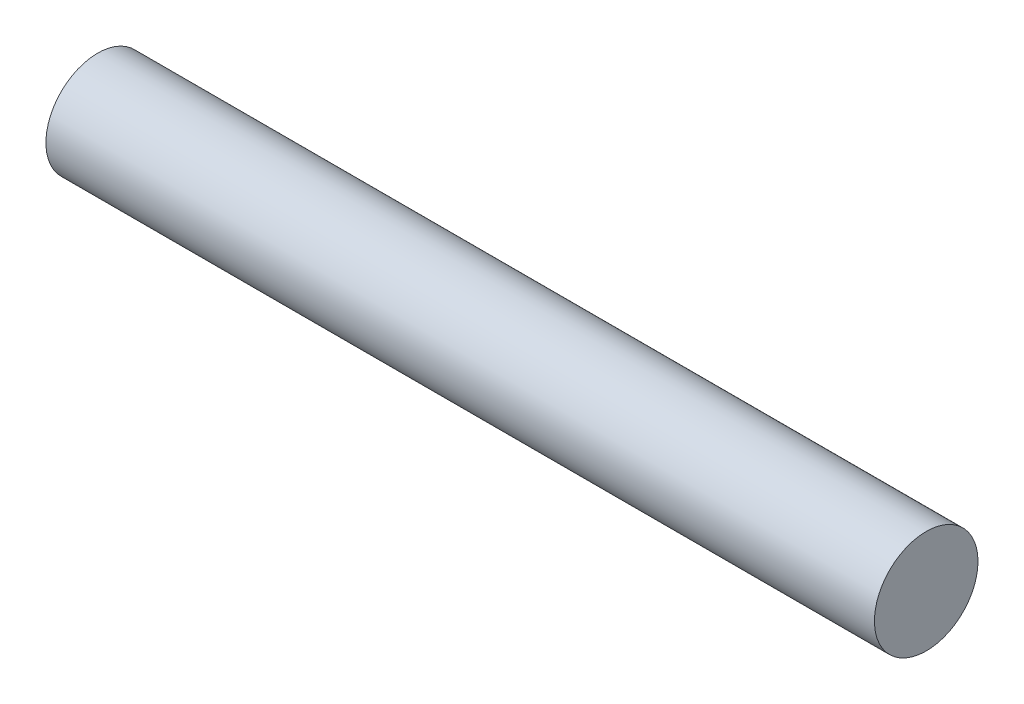
SolidWorks part; units mm, degrees
ref_plane "Plan de face" through (0, 0, 0) normal (0, 0, 1) x (1, 0, 0)
ref_plane "Plan de dessus" through (0, 0, 0) normal (0, 1, 0) x (1, 0, 0)
ref_plane "Plan de droite" through (0, 0, 0) normal (1, 0, 0) x (0, 0, -1)
sketch "Esquisse1" plane through (0, 0, 0) normal (1, 0, 0) x (0, 0, -1)
  circle A0 centre (0, 0) radius 2.5
extrude "Boss.-Extru.1" add sketch "Esquisse1" along normal blind 40
